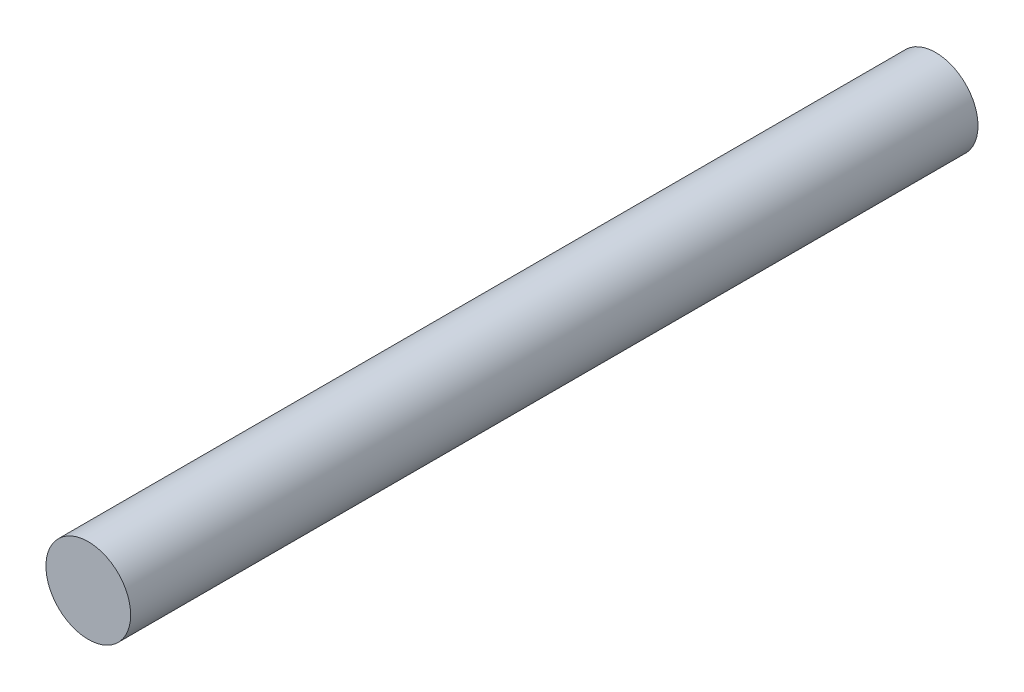
SolidWorks part; units mm, degrees
ref_plane "前视基准面" through (0, 0, 0) normal (0, 0, 1) x (1, 0, 0)
ref_plane "上视基准面" through (0, 0, 0) normal (0, 1, 0) x (1, 0, 0)
ref_plane "右视基准面" through (0, 0, 0) normal (1, 0, 0) x (0, 0, -1)
sketch "草图1" plane through (0, 0, 0) normal (0, 0, 1) x (1, 0, 0)
  circle A0 centre (0, 0) radius 1
extrude "凸台-拉伸1" add sketch "草图1" along normal mid plane 20
